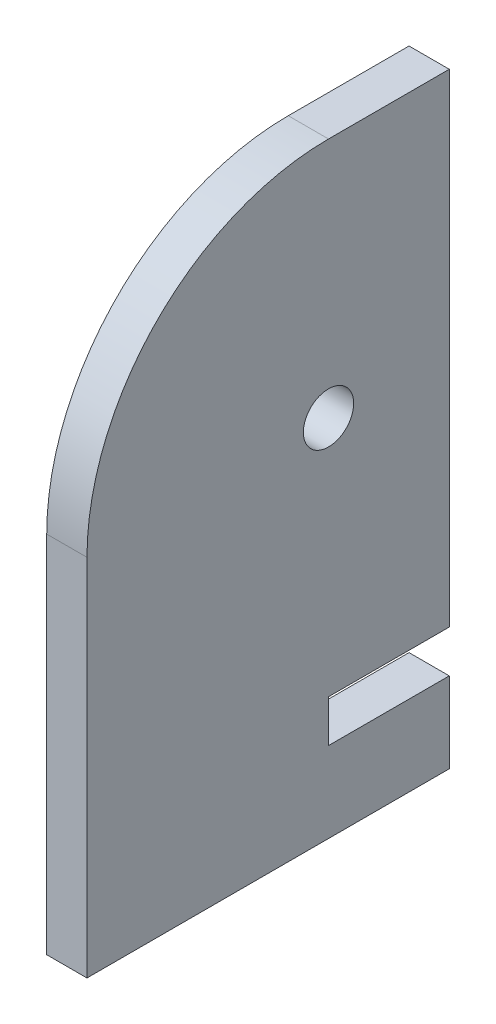
SolidWorks part; units mm, degrees
ref_plane "Front Plane" through (0, 0, 0) normal (0, 0, 1) x (1, 0, 0)
ref_plane "Top Plane" through (0, 0, 0) normal (0, 1, 0) x (1, 0, 0)
ref_plane "Right Plane" through (0, 0, 0) normal (1, 0, 0) x (0, 0, -1)
sketch "Sketch1" plane through (0, 0, 0) normal (1, 0, 0) x (0, 0, -1)
  line L0 (0, -76.2) -> (38.1, -76.2)
  line L1 (0, -76.2) -> (0, -89.535)
  line L2 (0, -89.535) -> (38.1, -89.535)
  line L3 (38.1, -89.535) -> (38.1, -114.935)
  line L4 (38.1, -114.935) -> (-76.2, -114.935)
  line L5 (-76.2, 0) -> (-76.2, -114.935)
  line L6 (38.1, -76.2) -> (38.1, 76.2)
  line L7 (38.1, 76.2) -> (0, 76.2)
  circle A0 centre (0, 0) radius 7.9375
  arc A1 (0, 76.2) -> (-76.2, 0) centre (0, 0) ccw
  dimension "D1" = 15.875
  dimension "D2" = 152.4
  dimension "D3" = 76.2
  dimension "D4" = 13.335
  dimension "D5" = 38.1
  dimension "D6" = 25.4
  dimension "D7" = 114.3
  dimension "D8" = 191.135
extrude "Boss-Extrude1" add sketch "Sketch1" along normal mid plane 12.7
